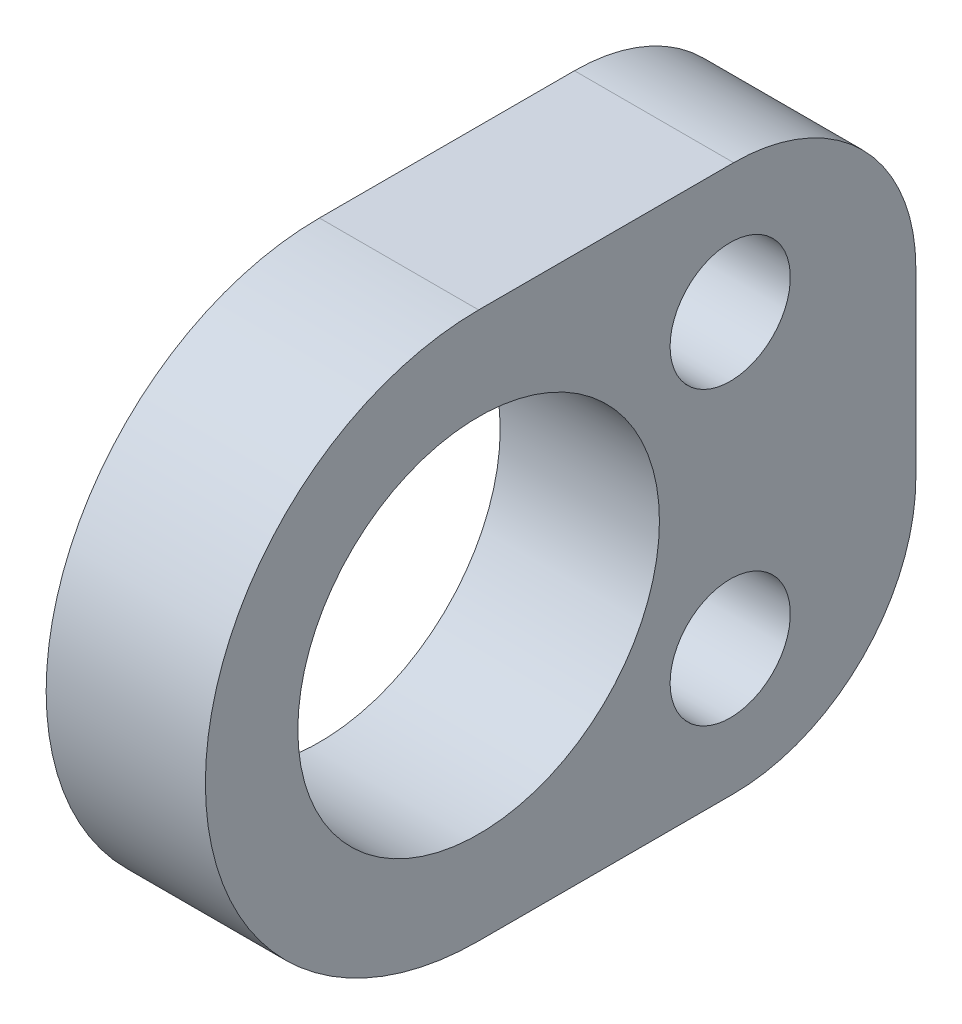
SolidWorks part; units mm, degrees
material "Plain Carbon Steel"
ref_plane "Front Plane" through (0, 0, 0) normal (0, 0, 1) x (1, 0, 0)
ref_plane "Top Plane" through (0, 0, 0) normal (0, 1, 0) x (1, 0, 0)
ref_plane "Right Plane" through (0, 0, 0) normal (1, 0, 0) x (0, 0, -1)
sketch "Sketch1" plane through (0, 0, 0) normal (1, 0, 0) x (0, 0, -1)
  line L0 (6.9051, 4) -> (6.9051, -4) construction
  line L1 (0, 7.5) -> (12, 7.5)
  line L2 (12, 7.5) -> (12, -7.5)
  line L3 (12, -7.5) -> (0, -7.5)
  arc A1 (6.9051, -4) -> (6.9051, 4) centre (0, 0) ccw construction
  circle A5 centre (0, 0) radius 4.9625
  arc A7 (0, 7.5) -> (0, -7.5) centre (0, 0) ccw
  point P21 (12, 0)
  dimension "D1" = 15
  dimension "D2" = 7.98
  dimension "D5" = 12
  dimension "D6" = 9.925
  dimension "D3" = 8
extrude "Boss-Extrude1" add sketch "Sketch1" along normal blind 4.37
fillet "Fillet1" radius 5 2 edges at (2.185, 7.5, -12) (2.185, -7.5, -12)
sketch "Sketch2" plane through (0, 0, 0) normal (-1, 0, 0) x (0, 0, 1)
  line L0 (-6.9051, 4) -> (-6.9051, -4) construction
  arc A0 (-6.9051, 4) -> (-6.9051, -4) centre (0, 0) ccw
  circle A1 centre (-6.9051, 4) radius 1.65
  circle A2 centre (-6.9051, -4) radius 1.65
  point P0 (-6.9051, 4)
  point P1 (-6.9051, -4)
  dimension "D1" = 7.98
  dimension "D2" = 3.3
extrude "Cut-Extrude1" cut sketch "Sketch2" against normal through all contours A0 L0 A1 | A2 L0 A0 | L0 A2 A0 | L0 A0 A1
